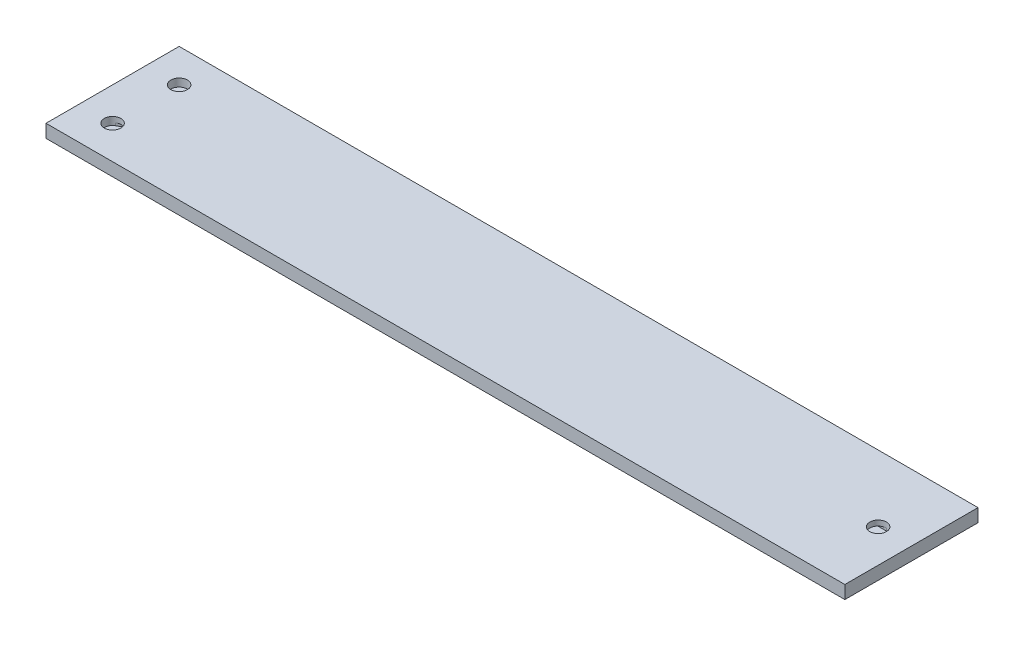
SolidWorks part; units mm, degrees
material "Glass"
ref_plane "Front Plane" through (0, 0, 0) normal (0, 0, 1) x (1, 0, 0)
ref_plane "Top Plane" through (0, 0, 0) normal (0, 1, 0) x (1, 0, 0)
ref_plane "Right Plane" through (0, 0, 0) normal (1, 0, 0) x (0, 0, -1)
sketch "Sketch1" plane through (0, 0, 0) normal (0, 1, 0) x (1, 0, 0)
  line L0 (0, 0) -> (-6.35, 0) construction
  line L1 (-44.45, -12.7) -> (31.75, -12.7)
  line L2 (-44.45, -12.7) -> (-44.45, 12.7) construction
  line L3 (-44.45, 12.7) -> (31.75, 12.7)
  line L4 (31.75, -12.7) -> (31.75, 12.7) construction
  line L5 (-44.45, -12.7) -> (31.75, 12.7) construction
  line L6 (-44.45, 12.7) -> (31.75, -12.7) construction
  line L7 (-44.45, 12.7) -> (-69.85, 12.7)
  line L8 (-69.85, 12.7) -> (-69.85, -12.7) construction
  line L9 (-69.85, -12.7) -> (-44.45, -12.7)
  line L10 (-69.85, 12.7) -> (-95.25, 12.7)
  line L11 (-95.25, 12.7) -> (-95.25, -12.7)
  line L12 (-95.25, -12.7) -> (-69.85, -12.7)
  line L13 (31.75, 12.7) -> (57.15, 12.7)
  line L14 (57.15, 12.7) -> (57.15, -12.7)
  line L15 (57.15, -12.7) -> (31.75, -12.7)
  point P0 (-6.35, 0)
  dimension "D1" = 25.4
  dimension "D2" = 76.2
  dimension "D3" = 6.35
  dimension "D4" = 25.4
  dimension "D5" = 25.4
  dimension "D6" = 25.4
extrude "Boss-Extrude1" add sketch "Sketch1" along normal blind 1
sketch "Sketch2" plane through (0, 1, 0) normal (0, 1, 0) x (1, 0, 0)
  line L0 (-95.25, 0) -> (57.15, 0) construction
  line L1 (57.15, -12.7) -> (57.15, 12.7) construction
  line L3 (-25.4, 0) -> (-18.0677, 4.2333)
  line L4 (-18.0677, 4.2333) -> (-11.7177, 4.2333)
  line L5 (-11.7177, 4.2333) -> (-8.0515, 6.35)
  line L6 (-8.0515, 6.35) -> (-1.7015, 6.35)
  line L7 (-11.7177, 4.2333) -> (-1.7015, 4.2333) construction
  line L8 (-11.7177, 4.2333) -> (-8.0515, 2.1167)
  line L9 (-8.0515, 2.1167) -> (-1.7015, 2.1167)
  line L10 (-11.7177, -4.2333) -> (-1.7015, -4.2333) construction
  line L11 (-8.0515, -2.1167) -> (-1.7015, -2.1167)
  line L12 (-11.7177, -4.2333) -> (-8.0515, -2.1167)
  line L13 (-8.0515, -6.35) -> (-1.7015, -6.35)
  line L14 (-11.7177, -4.2333) -> (-8.0515, -6.35)
  line L15 (-18.0677, -4.2333) -> (-11.7177, -4.2333)
  line L16 (-25.4, 0) -> (-18.0677, -4.2333)
  line L17 (-25.4, 0) -> (-31.75, 0)
  line L18 (-1.7015, 0) -> (-1.7015, 2.1167) construction
  line L21 (-1.7015, 2.1167) -> (-1.7015, 4.2333) construction
  line L24 (57.15, 12.7) -> (-95.25, 12.7) construction
  line L26 (-95.25, 12.7) -> (-95.25, -12.7) construction
  dimension "D1" = 6.35
  dimension "D2" = 60
  dimension "D4" = 6.35
  dimension "D3" = 63.5
sketch "Sketch5" plane through (0, 1, 0) normal (0, 1, 0) x (1, 0, 0)
  line L0 (-31.75, 0) -> (-25.4, 0) construction
  line L1 (-31.75, 1.5875) -> (-25.4, 1.5875)
  line L2 (-31.75, -1.5875) -> (-25.4, -1.5875)
  line L3 (-25.4, 0) -> (-18.0677, 4.2333) construction
  line L4 (-26.1937, 1.3748) -> (-18.8614, 5.6081)
  line L5 (-24.6063, -1.3748) -> (-17.2739, 2.8585)
  line L6 (-18.0677, 4.2333) -> (-11.7177, 4.2333) construction
  line L7 (-18.0677, 5.8208) -> (-11.7177, 5.8208)
  line L8 (-18.0677, 2.6458) -> (-11.7177, 2.6458)
  line L9 (-11.7177, 4.2333) -> (-8.0515, 6.35) construction
  line L10 (-12.5114, 5.6081) -> (-8.8452, 7.7248)
  line L11 (-10.9239, 2.8585) -> (-7.2577, 4.9752)
  line L12 (-8.0515, 6.35) -> (-1.7015, 6.35) construction
  line L13 (-8.0515, 7.9375) -> (-1.7015, 7.9375)
  line L14 (-8.0515, 4.7625) -> (-1.7015, 4.7625)
  line L16 (-1.7015, 4.2333) -> (-11.7177, 4.2333) construction
  line L17 (-1.7015, 0) -> (-33.3375, 0) construction
  line L18 (-8.0515, 2.1167) -> (-1.7015, 2.1167) construction
  line L19 (-8.0515, 0.5292) -> (-1.7015, 0.5292)
  line L20 (-8.0515, 3.7042) -> (-1.7015, 3.7042)
  line L21 (-11.7177, 4.2333) -> (-8.0515, 2.1167) construction
  line L22 (-12.5114, 2.8585) -> (-8.8452, 0.7419)
  line L23 (-10.9239, 5.6081) -> (-7.2577, 3.4915)
  line L24 (-25.4, 0) -> (-18.0677, -4.2333) construction
  line L25 (-26.1937, -1.3748) -> (-18.8614, -5.6081)
  line L26 (-24.6063, 1.3748) -> (-17.2739, -2.8585)
  line L27 (-18.0677, -4.2333) -> (-11.7177, -4.2333) construction
  line L28 (-18.0677, -5.8208) -> (-11.7177, -5.8208)
  line L29 (-18.0677, -2.6458) -> (-11.7177, -2.6458)
  line L30 (-11.7177, -4.2333) -> (-8.0515, -6.35) construction
  line L31 (-12.5114, -5.6081) -> (-8.8452, -7.7248)
  line L32 (-10.9239, -2.8585) -> (-7.2577, -4.9752)
  line L33 (-8.0515, -6.35) -> (-1.7015, -6.35) construction
  line L34 (-8.0515, -7.9375) -> (-1.7015, -7.9375)
  line L35 (-8.0515, -4.7625) -> (-1.7015, -4.7625)
  line L36 (-8.0515, -2.1167) -> (-1.7015, -2.1167) construction
  line L37 (-8.0515, -0.5292) -> (-1.7015, -0.5292)
  line L38 (-8.0515, -3.7042) -> (-1.7015, -3.7042)
  line L39 (-11.7177, -4.2333) -> (-8.0515, -2.1167) construction
  line L40 (-12.5114, -2.8585) -> (-8.8452, -0.7419)
  line L41 (-10.9239, -5.6081) -> (-7.2577, -3.4915)
  arc A0 (-31.75, 1.5875) -> (-31.75, -1.5875) centre (-31.75, 0) ccw
  arc A1 (-25.4, -1.5875) -> (-25.4, 1.5875) centre (-25.4, 0) ccw
  arc A2 (-26.1937, 1.3748) -> (-24.6063, -1.3748) centre (-25.4, 0) ccw
  arc A3 (-17.2739, 2.8585) -> (-18.8614, 5.6081) centre (-18.0677, 4.2333) ccw
  arc A4 (-18.0677, 5.8208) -> (-18.0677, 2.6458) centre (-18.0677, 4.2333) ccw
  arc A5 (-11.7177, 2.6458) -> (-11.7177, 5.8208) centre (-11.7177, 4.2333) ccw
  arc A6 (-12.5114, 5.6081) -> (-10.9239, 2.8585) centre (-11.7177, 4.2333) ccw
  arc A7 (-7.2577, 4.9752) -> (-8.8452, 7.7248) centre (-8.0515, 6.35) ccw
  arc A8 (-8.0515, 7.9375) -> (-8.0515, 4.7625) centre (-8.0515, 6.35) ccw
  arc A9 (-1.7015, 4.7625) -> (-1.7015, 7.9375) centre (-1.7015, 6.35) ccw
  arc A10 (-8.0515, 0.5292) -> (-8.0515, 3.7042) centre (-8.0515, 2.1167) cw
  arc A11 (-1.7015, 3.7042) -> (-1.7015, 0.5292) centre (-1.7015, 2.1167) cw
  arc A12 (-12.5114, 2.8585) -> (-10.9239, 5.6081) centre (-11.7177, 4.2333) cw
  arc A13 (-7.2577, 3.4915) -> (-8.8452, 0.7419) centre (-8.0515, 2.1167) cw
  arc A14 (-26.1937, -1.3748) -> (-24.6063, 1.3748) centre (-25.4, 0) cw
  arc A15 (-17.2739, -2.8585) -> (-18.8614, -5.6081) centre (-18.0677, -4.2333) cw
  arc A16 (-18.0677, -5.8208) -> (-18.0677, -2.6458) centre (-18.0677, -4.2333) cw
  arc A17 (-11.7177, -2.6458) -> (-11.7177, -5.8208) centre (-11.7177, -4.2333) cw
  arc A18 (-12.5114, -5.6081) -> (-10.9239, -2.8585) centre (-11.7177, -4.2333) cw
  arc A19 (-7.2577, -4.9752) -> (-8.8452, -7.7248) centre (-8.0515, -6.35) cw
  arc A20 (-8.0515, -7.9375) -> (-8.0515, -4.7625) centre (-8.0515, -6.35) cw
  arc A21 (-1.7015, -4.7625) -> (-1.7015, -7.9375) centre (-1.7015, -6.35) cw
  arc A22 (-8.0515, -0.5292) -> (-8.0515, -3.7042) centre (-8.0515, -2.1167) ccw
  arc A23 (-1.7015, -3.7042) -> (-1.7015, -0.5292) centre (-1.7015, -2.1167) ccw
  arc A24 (-12.5114, -2.8585) -> (-10.9239, -5.6081) centre (-11.7177, -4.2333) ccw
  arc A25 (-7.2577, -3.4915) -> (-8.8452, -0.7419) centre (-8.0515, -2.1167) ccw
  point P4 (-28.575, 0)
  point P9 (-21.7338, 2.1167)
  point P17 (-14.8927, 4.2333)
  point P25 (-9.8846, 5.2917)
  point P33 (-4.8765, 6.35)
  point P41 (-14.8927, 5.8208)
  point P50 (-4.8765, 2.1167)
  point P56 (-9.8846, 3.175)
  point P63 (-21.7338, -2.1167)
  point P70 (-14.8927, -4.2333)
  point P77 (-9.8846, -5.2917)
  point P84 (-4.8765, -6.35)
  point P91 (-4.8765, -2.1167)
  point P98 (-9.8846, -3.175)
  dimension "D1" = 3.175
  dimension "D2" = 3.175
  dimension "D3" = 3.175
  dimension "D4" = 3.175
  dimension "D5" = 3.175
extrude "Boss-Extrude3" add sketch "Sketch5" along normal blind 0.5
sketch "Sketch6" plane through (0, 1.5, 0) normal (0, 1, 0) x (1, 0, 0)
  line L0 (-95.25, 0) -> (57.15, 0) construction
  line L1 (10.3296, -7.9375) -> (-1.7015, -7.9375)
  line L2 (10.9985, -7.9375) -> (10.9985, 7.9375)
  line L3 (10.3296, 7.9375) -> (-1.7015, 7.9375)
  line L4 (-1.7015, -7.9375) -> (-1.7015, 7.9375)
  line L5 (10.9985, -7.9375) -> (-1.7015, 7.9375) construction
  line L6 (10.9985, 7.9375) -> (-1.7015, -7.9375) construction
  line L7 (11.6106, 7.6676) -> (25.4, 1.5875)
  line L8 (25.4, 1.5875) -> (25.4, -1.5875)
  line L9 (25.4, -1.5875) -> (11.6106, -7.6676)
  line L12 (57.15, -12.7) -> (57.15, 12.7) construction
  line L13 (25.4, 0) -> (50.8, 0) construction
  line L14 (25.4, 1.5875) -> (50.8, 1.5875)
  line L15 (25.4, -1.5875) -> (50.8, -1.5875)
  circle A0 centre (25.4, 0) radius 1.5875
  arc A1 (10.3296, -7.9375) -> (11.6106, -7.6676) centre (10.3296, -4.7625) ccw
  arc A2 (10.3296, 7.9375) -> (11.6106, 7.6676) centre (10.3296, 4.7625) cw
  arc A3 (25.4, 1.5875) -> (25.4, -1.5875) centre (25.4, 0) ccw
  arc A4 (50.8, -1.5875) -> (50.8, 1.5875) centre (50.8, 0) ccw
  point P0 (4.6485, 0)
  point P11 (38.1, 0)
  arc M5 (-1.7015, -0.5292) -> (-1.7015, -3.7042) centre (-1.7015, -2.1167) cw
  arc M10 (-1.7015, -4.7625) -> (-1.7015, -7.9375) centre (-1.7015, -6.35) cw
  arc M26 (-1.7015, 7.9375) -> (-1.7015, 4.7625) centre (-1.7015, 6.35) cw
  arc M31 (-1.7015, 3.7042) -> (-1.7015, 0.5292) centre (-1.7015, 2.1167) cw
  dimension "D3" = 3.175
  dimension "D4" = 3.175
  dimension "D5" = 1.5875
  dimension "D1" = 12.7
  dimension "D2" = 31.75
  dimension "D6" = 6.35
extrude "Cut-Extrude1" cut sketch "Sketch6" against normal blind 0.5 contours A2 L3 L4 L1 A1 L2 M26 M31 M5 M10 | A2 L2 A1 L9 A0 L7 | L8 A0 | L8 A0 | L15 A4 L14 A0
sketch "Sketch7" plane through (0, 1.5, 0) normal (0, 1, 0) x (1, 0, 0)
  line L0 (-31.75, 0) -> (-31.75, 6.35)
  line L1 (-31.75, 6.35) -> (-38.1, 6.35)
  line L2 (-38.1, 6.35) -> (-38.1, -6.35)
  line L3 (-38.1, -6.35) -> (-44.45, -6.35)
  line L4 (-44.45, -6.35) -> (-44.45, 0)
  line L5 (-95.25, 0) -> (57.15, 0) construction
  line L6 (57.15, 12.7) -> (-95.25, 12.7) construction
  line L7 (-44.45, 0) -> (-44.45, -6.35) construction
  line L8 (-95.25, -12.7) -> (57.15, -12.7) construction
  line L9 (-42.8625, 0) -> (-42.8625, -6.35)
  line L10 (-46.0375, 0) -> (-46.0375, -6.35)
  line L11 (-44.45, -6.35) -> (-38.1, -6.35) construction
  line L12 (-44.45, -4.7625) -> (-38.1, -4.7625)
  line L13 (-44.45, -7.9375) -> (-38.1, -7.9375)
  line L14 (-38.1, -6.35) -> (-38.1, 6.35) construction
  line L15 (-39.6875, -6.35) -> (-39.6875, 6.35)
  line L16 (-36.5125, -6.35) -> (-36.5125, 6.35)
  line L17 (-38.1, 6.35) -> (-31.75, 6.35) construction
  line L18 (-38.1, 7.9375) -> (-31.75, 7.9375)
  line L19 (-38.1, 4.7625) -> (-31.75, 4.7625)
  line L20 (-31.75, 6.35) -> (-31.75, 0) construction
  line L21 (-30.1625, 6.35) -> (-30.1625, 0)
  line L22 (-33.3375, 6.35) -> (-33.3375, 0)
  line L23 (-58.7375, 0) -> (-58.7375, -6.35)
  line L24 (-55.5625, 0) -> (-55.5625, -6.35)
  line L25 (-57.15, -7.9375) -> (-50.8, -7.9375)
  line L26 (-57.15, -4.7625) -> (-50.8, -4.7625)
  line L27 (-49.2125, -6.35) -> (-49.2125, 6.35)
  line L28 (-52.3875, -6.35) -> (-52.3875, 6.35)
  line L29 (-50.8, 4.7625) -> (-44.45, 4.7625)
  line L30 (-50.8, 7.9375) -> (-44.45, 7.9375)
  line L31 (-46.0375, 6.35) -> (-46.0375, 0)
  line L32 (-42.8625, 6.35) -> (-42.8625, 0)
  line L33 (-57.15, 0) -> (-57.15, -6.35) construction
  line L34 (-57.15, -6.35) -> (-50.8, -6.35) construction
  line L35 (-50.8, -6.35) -> (-50.8, 6.35) construction
  line L36 (-50.8, 6.35) -> (-44.45, 6.35) construction
  line L37 (-44.45, 6.35) -> (-44.45, 0) construction
  line L38 (-71.4375, 0) -> (-71.4375, -6.35)
  line L39 (-68.2625, 0) -> (-68.2625, -6.35)
  line L40 (-69.85, -7.9375) -> (-63.5, -7.9375)
  line L41 (-69.85, -4.7625) -> (-63.5, -4.7625)
  line L42 (-61.9125, -6.35) -> (-61.9125, 6.35)
  line L43 (-65.0875, -6.35) -> (-65.0875, 6.35)
  line L44 (-63.5, 4.7625) -> (-57.15, 4.7625)
  line L45 (-63.5, 7.9375) -> (-57.15, 7.9375)
  line L46 (-58.7375, 6.35) -> (-58.7375, 0)
  line L47 (-55.5625, 6.35) -> (-55.5625, 0)
  line L48 (-69.85, 0) -> (-69.85, -6.35) construction
  line L49 (-69.85, -6.35) -> (-63.5, -6.35) construction
  line L50 (-63.5, -6.35) -> (-63.5, 6.35) construction
  line L51 (-63.5, 6.35) -> (-57.15, 6.35) construction
  line L52 (-57.15, 6.35) -> (-57.15, 0) construction
  line L53 (-69.85, 0) -> (-77.9015, 0) construction
  line L54 (-69.85, -1.5875) -> (-77.9015, -1.5875)
  line L55 (-69.85, 1.5875) -> (-77.9015, 1.5875)
  line L56 (-77.9015, 0) -> (-88.9, 6.35) construction
  line L57 (-78.6952, -1.3748) -> (-89.6938, 4.9752)
  line L58 (-77.1077, 1.3748) -> (-88.1063, 7.7248)
  line L59 (-95.25, 0) -> (-77.9015, 0) construction
  line L60 (-95.25, 12.7) -> (-95.25, -12.7) construction
  line L61 (-77.9015, 0) -> (-88.9, -6.35) construction
  line L62 (-78.6952, 1.3748) -> (-89.6938, -4.9752)
  line L63 (-77.1077, -1.3748) -> (-88.1063, -7.7248)
  line L64 (57.15, 12.7) -> (-95.25, 12.7) construction
  arc A0 (-42.8625, 0) -> (-46.0375, 0) centre (-44.45, 0) ccw
  arc A1 (-46.0375, -6.35) -> (-42.8625, -6.35) centre (-44.45, -6.35) ccw
  arc A2 (-44.45, -4.7625) -> (-44.45, -7.9375) centre (-44.45, -6.35) ccw
  arc A3 (-38.1, -7.9375) -> (-38.1, -4.7625) centre (-38.1, -6.35) ccw
  arc A4 (-39.6875, -6.35) -> (-36.5125, -6.35) centre (-38.1, -6.35) ccw
  arc A5 (-36.5125, 6.35) -> (-39.6875, 6.35) centre (-38.1, 6.35) ccw
  arc A6 (-38.1, 7.9375) -> (-38.1, 4.7625) centre (-38.1, 6.35) ccw
  arc A7 (-31.75, 4.7625) -> (-31.75, 7.9375) centre (-31.75, 6.35) ccw
  arc A8 (-30.1625, 6.35) -> (-33.3375, 6.35) centre (-31.75, 6.35) ccw
  arc A9 (-33.3375, 0) -> (-30.1625, 0) centre (-31.75, 0) ccw
  arc A10 (-55.5625, 0) -> (-58.7375, 0) centre (-57.15, 0) ccw
  arc A11 (-58.7375, -6.35) -> (-55.5625, -6.35) centre (-57.15, -6.35) ccw
  arc A12 (-57.15, -4.7625) -> (-57.15, -7.9375) centre (-57.15, -6.35) ccw
  arc A13 (-50.8, -7.9375) -> (-50.8, -4.7625) centre (-50.8, -6.35) ccw
  arc A14 (-52.3875, -6.35) -> (-49.2125, -6.35) centre (-50.8, -6.35) ccw
  arc A15 (-49.2125, 6.35) -> (-52.3875, 6.35) centre (-50.8, 6.35) ccw
  arc A16 (-50.8, 7.9375) -> (-50.8, 4.7625) centre (-50.8, 6.35) ccw
  arc A17 (-44.45, 4.7625) -> (-44.45, 7.9375) centre (-44.45, 6.35) ccw
  arc A18 (-42.8625, 6.35) -> (-46.0375, 6.35) centre (-44.45, 6.35) ccw
  arc A19 (-46.0375, 0) -> (-42.8625, 0) centre (-44.45, 0) ccw
  arc A20 (-68.2625, 0) -> (-71.4375, 0) centre (-69.85, 0) ccw
  arc A21 (-71.4375, -6.35) -> (-68.2625, -6.35) centre (-69.85, -6.35) ccw
  arc A22 (-69.85, -4.7625) -> (-69.85, -7.9375) centre (-69.85, -6.35) ccw
  arc A23 (-63.5, -7.9375) -> (-63.5, -4.7625) centre (-63.5, -6.35) ccw
  arc A24 (-65.0875, -6.35) -> (-61.9125, -6.35) centre (-63.5, -6.35) ccw
  arc A25 (-61.9125, 6.35) -> (-65.0875, 6.35) centre (-63.5, 6.35) ccw
  arc A26 (-63.5, 7.9375) -> (-63.5, 4.7625) centre (-63.5, 6.35) ccw
  arc A27 (-57.15, 4.7625) -> (-57.15, 7.9375) centre (-57.15, 6.35) ccw
  arc A28 (-55.5625, 6.35) -> (-58.7375, 6.35) centre (-57.15, 6.35) ccw
  arc A29 (-58.7375, 0) -> (-55.5625, 0) centre (-57.15, 0) ccw
  arc A30 (-69.85, -1.5875) -> (-69.85, 1.5875) centre (-69.85, 0) ccw
  arc A31 (-77.9015, 1.5875) -> (-77.9015, -1.5875) centre (-77.9015, 0) ccw
  arc A32 (-78.6952, -1.3748) -> (-77.1077, 1.3748) centre (-77.9015, 0) ccw
  arc A33 (-88.1063, 7.7248) -> (-89.6938, 4.9752) centre (-88.9, 6.35) ccw
  arc A34 (-78.6952, 1.3748) -> (-77.1077, -1.3748) centre (-77.9015, 0) cw
  arc A35 (-88.1063, -7.7248) -> (-89.6938, -4.9752) centre (-88.9, -6.35) cw
  point P13 (-44.45, -3.175)
  point P18 (-41.275, -6.35)
  point P24 (-38.1, 0)
  point P30 (-34.925, 6.35)
  point P36 (-31.75, 3.175)
  point P49 (-57.15, -3.175)
  point P54 (-53.975, -6.35)
  point P60 (-50.8, 0)
  point P66 (-47.625, 6.35)
  point P72 (-44.45, 3.175)
  point P84 (-69.85, -3.175)
  point P89 (-66.675, -6.35)
  point P95 (-63.5, 0)
  point P101 (-60.325, 6.35)
  point P107 (-57.15, 3.175)
  point P114 (-73.8757, 0)
  point P119 (-83.4007, 3.175)
  point P131 (-83.4007, -3.175)
  dimension "D4" = 1.5875
  dimension "D5" = 1.5875
  dimension "D6" = 1.5875
  dimension "D7" = 1.5875
  dimension "D8" = 1.5875
  dimension "D10" = 1.5875
  dimension "D11" = 1.5875
  dimension "D1" = 6.35
  dimension "D2" = 6.35
  dimension "D3" = 6.35
  dimension "D12" = 6.35
  dimension "D13" = 6.35
  dimension "D14" = 60
  dimension "D9" = 3
extrude "Cut-Extrude2" cut sketch "Sketch7" against normal blind 0.5 contours A22 L41 L39 A20 L38 | L41 A22 A21 L39 | A24 L43 L41 L39 A21 L40 | A27 L44 L46 A10 L47 | L26 A13 L25 A12 | L28 A15 L27 A14 | L29 A17 L30 A16 | L31 A19 L32 A18 | L10 A1 L9 A0 | L12 A3 L13 A2 | L15 A5 L16 A4 | L19 A7 L18 A6 | L22 A9 L21 A8 | L54 A31 L55 A30 | L63 A35 L62 A34 | L57 A33 L58 A32
sketch "Sketch8" plane through (0, 1.5, 0) normal (0, 1, 0) x (1, 0, 0)
  line L0 (57.15, -12.7) -> (57.15, 12.7) construction
  line L1 (-95.25, 12.7) -> (57.15, 12.7)
  line L2 (-95.25, 12.7) -> (-95.25, -12.7)
  line L3 (-95.25, -12.7) -> (57.15, -12.7)
  line L4 (57.15, 12.7) -> (57.15, -12.7)
extrude "Boss-Extrude4" add sketch "Sketch8" along normal blind 1
sketch "Sketch9" plane through (0, 2.5, 0) normal (0, 1, 0) x (1, 0, 0)
  circle A0 centre (-88.9, 6.35) radius 1.5875
  circle A1 centre (-88.9, -6.35) radius 1.5875
  circle A2 centre (50.8, 0) radius 1.5875
extrude "Cut-Extrude8" cut sketch "Sketch9" against normal up to next
equation "\"channel_width\"=0.0625"
equation "\"D2@Sketch5\"=\"channel_width\"*2"
equation "\"D3@Sketch5\"=\"channel_width\"*2"
equation "\"D4@Sketch5\"=\"channel_width\"*2"
equation "\"D5@Sketch5\"=\"channel_width\"*2"
equation "\"D4@Sketch7\"=\"channel_width\""
equation "\"D7@Sketch7\"=\"channel_width\""
equation "\"D8@Sketch7\"=\"channel_width\""
equation "\"D11@Sketch7\"=\"channel_width\""
equation "\"D5@Sketch6\"=\"channel_width\""
equation "\"D8@Sketch2\"=\"channel_width\""
equation "\"D7@Sketch2\"=\"channel_width\""
equation "\"D6@Sketch2\"=\"channel_width\""
